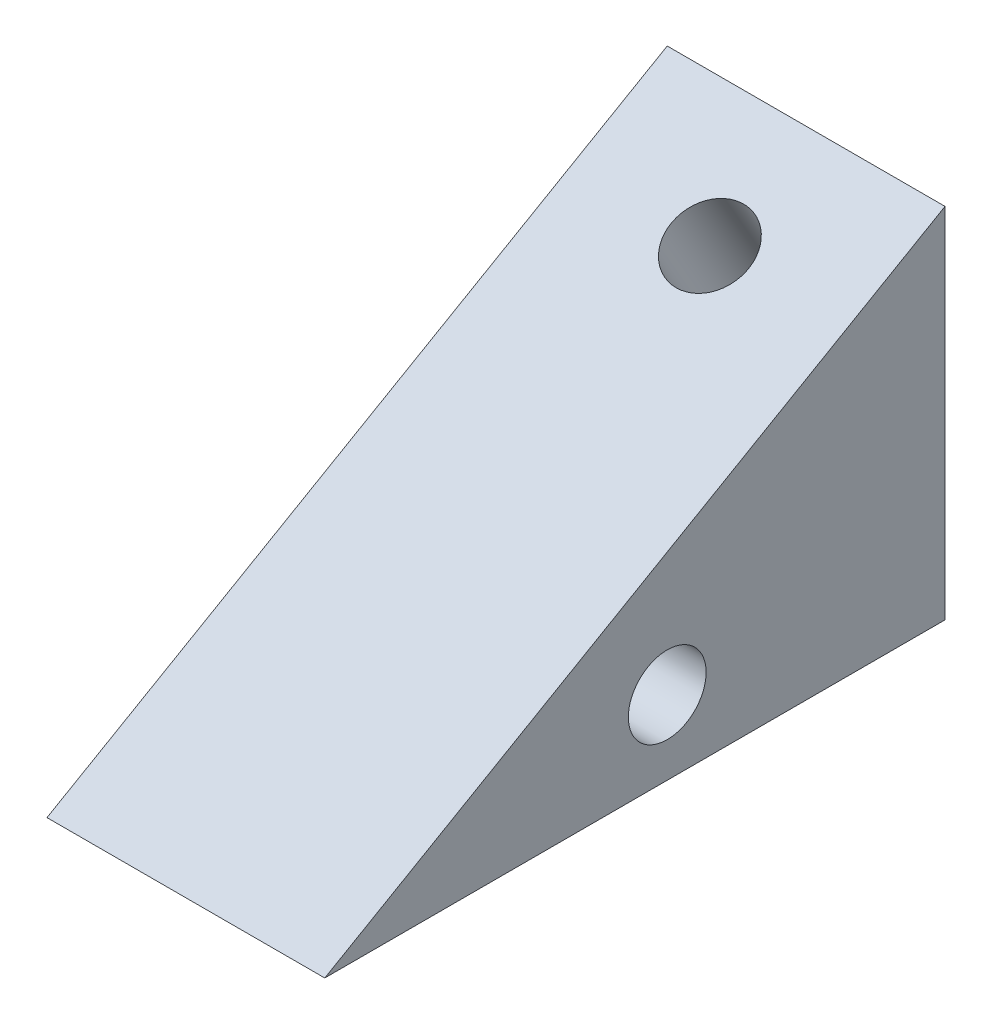
SolidWorks part; units mm, degrees
ref_plane "Front Plane" through (0, 0, 0) normal (0, 0, 1) x (1, 0, 0)
ref_plane "Top Plane" through (0, 0, 0) normal (0, 1, 0) x (1, 0, 0)
ref_plane "Right Plane" through (0, 0, 0) normal (1, 0, 0) x (0, 0, -1)
sketch "Sketch3" plane through (0, 0, 0) normal (1, 0, 0) x (0, 0, -1)
  line L0 (0, 0) -> (-33.4905, 0)
  line L1 (-33.4905, 0) -> (0, 19.3357)
  line L2 (0, 19.3357) -> (0, 0)
  dimension "D1" = 30
extrude "Boss-Extrude1" add sketch "Sketch3" along normal blind 15
hole_wizard "M5x0.8 Tapped Hole1" positions "Sketch4" profile "Sketch5" tap size "M5x0.8" standard "ANSI Metric" end condition through all
sketch "Sketch4" plane through (15, 0, 0) normal (1, 0, 0) x (0, 0, -1)
  line L0 (-33.4905, 0) -> (0, 0) construction
  line L1 (0, 0) -> (0, 19.3357) construction
  point P0 (-15, 4)
  dimension "D1" = 4
  dimension "D2" = 15
sketch "Sketch5" plane through (15, 4, 15) normal (0, 1, 0) x (0, 0, -1)
  line L0 (0, 0) -> (0, 15)
  line L1 (0, 15) -> (2.1, 15)
  line L2 (2.1, 15) -> (2.1, 0)
  line L5 (2.1, 0) -> (0, 0)
  line L11 (0, -6.35) -> (0, 107.95) construction
  dimension "Thru Tap Drill Dia." = 4.2
  dimension "Thru Tap Drill Depth" = 15
hole_wizard "M5x0.8 Tapped Hole2" positions "Sketch6" profile "Sketch7" tap size "M5x0.8" standard "ANSI Metric" end condition through all
sketch "Sketch6" plane through (0, 14.5018, 8.3726) normal (0, 0.866, 0.5) x (1, 0, 0)
  line L0 (0, 9.6679) -> (0, -29.0036) construction
  line L3 (15, 9.6679) -> (0, 9.6679) construction
  point P0 (7.5, 3.6679)
  point P3 (0, 0)
  dimension "D1" = 7.5
  dimension "D2" = 6
sketch "Sketch7" plane through (7.5, 16.3357, 5.1962) normal (1, 0, 0) x (0, -0.5, 0.866)
  line L0 (0, 0) -> (0, 16.7452)
  line L1 (0, 16.7452) -> (2.1, 16.7452)
  line L2 (2.1, 16.7452) -> (2.1, 0)
  line L5 (2.1, 0) -> (0, 0)
  line L11 (0, -6.35) -> (0, 107.95) construction
  dimension "Thru Tap Drill Dia." = 4.2
  dimension "Thru Tap Drill Depth" = 16.7452
